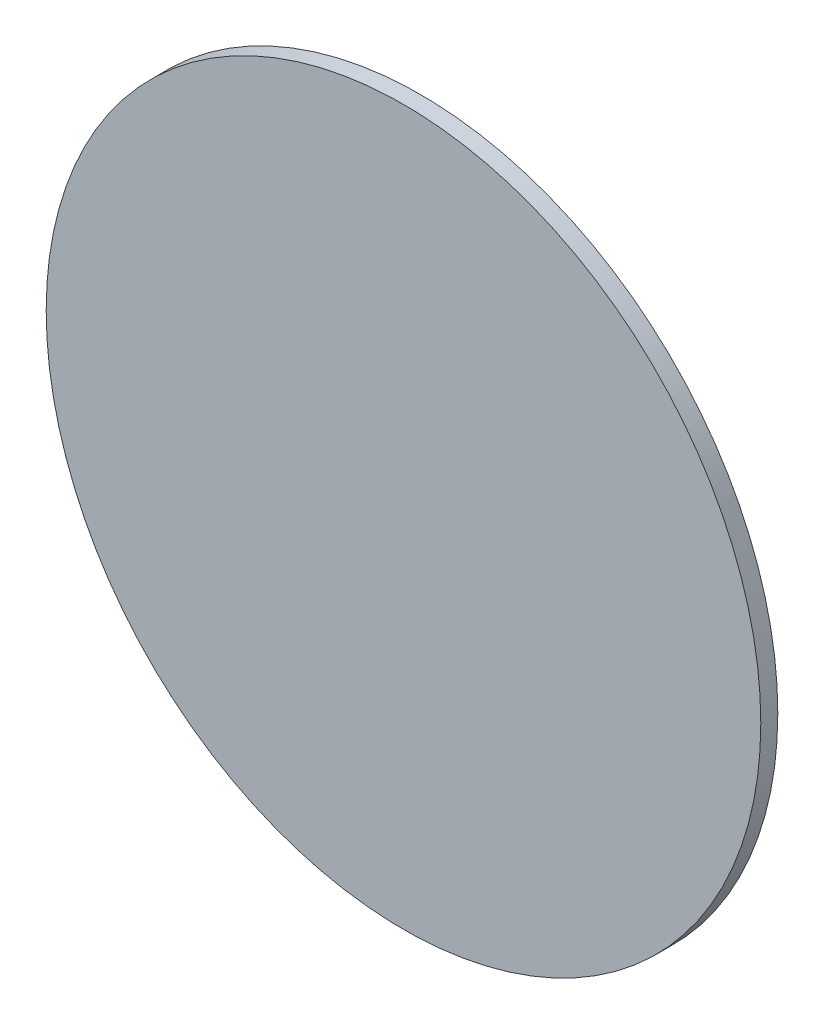
SolidWorks part; units mm, degrees
ref_plane "Plano frontal" through (0, 0, 0) normal (0, 0, 1) x (1, 0, 0)
ref_plane "Plano superior" through (0, 0, 0) normal (0, 1, 0) x (1, 0, 0)
ref_plane "Plano direito" through (0, 0, 0) normal (1, 0, 0) x (0, 0, -1)
sketch "Esboço1" plane through (0, 0, 0) normal (0, 0, 1) x (1, 0, 0)
  circle A0 centre (0, 0) radius 21
  dimension "D1" = 42
extrude "Ressalto-extrusão1" add sketch "Esboço1" along normal blind 1
